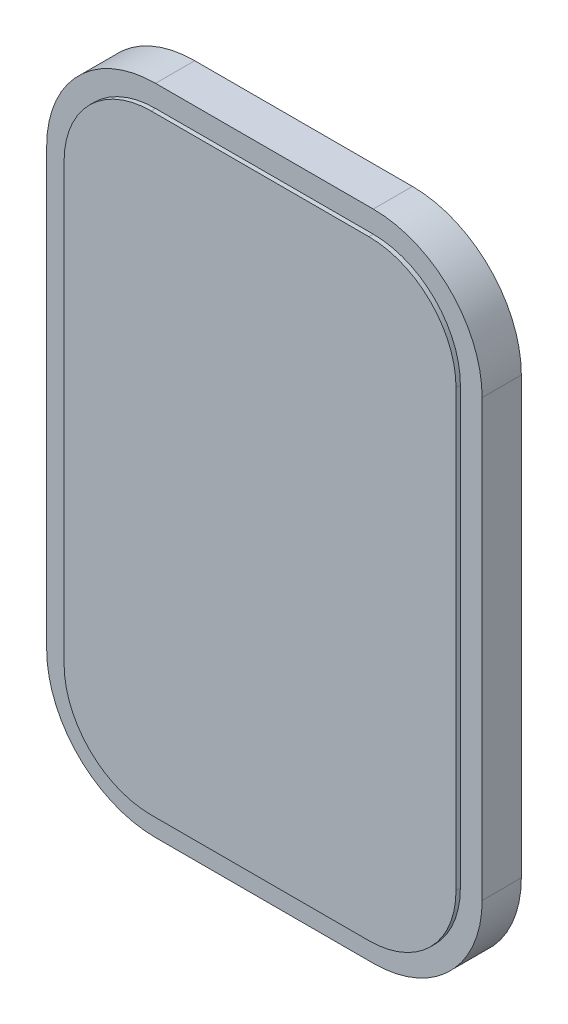
SolidWorks part; units mm, degrees
ref_plane "Front Plane" through (0, 0, 0) normal (0, 0, 1) x (1, 0, 0)
ref_plane "Top Plane" through (0, 0, 0) normal (0, 1, 0) x (1, 0, 0)
ref_plane "Right Plane" through (0, 0, 0) normal (1, 0, 0) x (0, 0, -1)
sketch "Sketch1" plane through (0, 0, 0) normal (0, 0, 1) x (1, 0, 0)
  line L1 (-12.7, -19.05) -> (12.7, -19.05)
  line L2 (-12.7, -19.05) -> (-12.7, 19.05)
  line L3 (-12.7, 19.05) -> (12.7, 19.05)
  line L4 (12.7, -19.05) -> (12.7, 19.05)
  line L5 (-12.7, -19.05) -> (12.7, 19.05) construction
  line L6 (-12.7, 19.05) -> (12.7, -19.05) construction
  point P0 (0, 0)
  dimension "D1" = 25.4
  dimension "D2" = 38.1
extrude "Boss-Extrude1" add sketch "Sketch1" along normal blind 2.54
fillet "Fillet1" radius 6.35 4 edges at (12.7, -19.05, 1.27) (12.7, 19.05, 1.27) (-12.7, -19.05, 1.27) (-12.7, 19.05, 1.27)
sketch "Sketch2" plane through (0, 0, 2.54) normal (0, 0, 1) x (1, 0, 0)
  line L0 (-11.43, 12.7) -> (-11.43, -12.7)
  line L1 (-6.35, -17.78) -> (6.35, -17.78)
  line L2 (11.43, -12.7) -> (11.43, 12.7)
  line L3 (6.35, 17.78) -> (-6.35, 17.78)
  line L4 (-6.35, -19.05) -> (6.35, -19.05)
  line L5 (12.7, -12.7) -> (12.7, 12.7)
  line L6 (6.35, 19.05) -> (-6.35, 19.05)
  line L7 (-12.7, 12.7) -> (-12.7, -12.7)
  line L8 (-6.35, -19.05) -> (6.35, -19.05)
  line L9 (12.7, -12.7) -> (12.7, 12.7)
  line L10 (6.35, 19.05) -> (-6.35, 19.05)
  line L11 (-12.7, 12.7) -> (-12.7, -12.7)
  arc A1 (-6.35, 17.78) -> (-11.43, 12.7) centre (-6.35, 12.7) ccw
  arc A2 (-11.43, -12.7) -> (-6.35, -17.78) centre (-6.35, -12.7) ccw
  arc A3 (6.35, -17.78) -> (11.43, -12.7) centre (6.35, -12.7) ccw
  arc A4 (11.43, 12.7) -> (6.35, 17.78) centre (6.35, 12.7) ccw
  arc A5 (6.35, -19.05) -> (12.7, -12.7) centre (6.35, -12.7) ccw
  arc A6 (12.7, 12.7) -> (6.35, 19.05) centre (6.35, 12.7) ccw
  arc A7 (-6.35, 19.05) -> (-12.7, 12.7) centre (-6.35, 12.7) ccw
  arc A8 (-12.7, -12.7) -> (-6.35, -19.05) centre (-6.35, -12.7) ccw
  arc A9 (6.35, -19.05) -> (12.7, -12.7) centre (6.35, -12.7) ccw
  arc A10 (12.7, 12.7) -> (6.35, 19.05) centre (6.35, 12.7) ccw
  arc A11 (-6.35, 19.05) -> (-12.7, 12.7) centre (-6.35, 12.7) ccw
  arc A12 (-12.7, -12.7) -> (-6.35, -19.05) centre (-6.35, -12.7) ccw
  dimension "D1" = 0
  dimension "D2" = 1.27
extrude "Cut-Extrude1" cut sketch "Sketch2" against normal blind 0.254
sketch "Sketch3" plane through (0, 0, 2.54) normal (0, 0, 1) x (1, 0, 0)
  line L0 (-10.922, 12.7) -> (-10.922, -12.7)
  line L1 (-6.35, -17.272) -> (6.35, -17.272)
  line L2 (10.922, -12.7) -> (10.922, 12.7)
  line L3 (6.35, 17.272) -> (-6.35, 17.272)
  line L4 (-11.43, 12.7) -> (-11.43, -12.7)
  line L5 (-6.35, -17.78) -> (6.35, -17.78)
  line L6 (11.43, -12.7) -> (11.43, 12.7)
  line L7 (6.35, 17.78) -> (-6.35, 17.78)
  line L8 (-11.43, 12.7) -> (-11.43, -12.7)
  line L9 (-6.35, -17.78) -> (6.35, -17.78)
  line L10 (11.43, -12.7) -> (11.43, 12.7)
  line L11 (6.35, 17.78) -> (-6.35, 17.78)
  line L12 (-6.35, 17.272) -> (-6.35, -12.192)
  line L13 (-6.35, -12.192) -> (-10.922, -12.192)
  line L14 (-10.922, -12.7) -> (10.922, -12.7)
  arc A0 (-6.35, 17.272) -> (-10.922, 12.7) centre (-6.35, 12.7) ccw
  arc A1 (-10.922, -12.7) -> (-6.35, -17.272) centre (-6.35, -12.7) ccw
  arc A2 (6.35, -17.272) -> (10.922, -12.7) centre (6.35, -12.7) ccw
  arc A3 (10.922, 12.7) -> (6.35, 17.272) centre (6.35, 12.7) ccw
  arc A4 (-6.35, 17.78) -> (-11.43, 12.7) centre (-6.35, 12.7) ccw
  arc A5 (-11.43, -12.7) -> (-6.35, -17.78) centre (-6.35, -12.7) ccw
  arc A6 (6.35, -17.78) -> (11.43, -12.7) centre (6.35, -12.7) ccw
  arc A7 (11.43, 12.7) -> (6.35, 17.78) centre (6.35, 12.7) ccw
  arc A8 (-6.35, 17.78) -> (-11.43, 12.7) centre (-6.35, 12.7) ccw
  arc A9 (-11.43, -12.7) -> (-6.35, -17.78) centre (-6.35, -12.7) ccw
  arc A10 (6.35, -17.78) -> (11.43, -12.7) centre (6.35, -12.7) ccw
  arc A11 (11.43, 12.7) -> (6.35, 17.78) centre (6.35, 12.7) ccw
  dimension "D3" = 0.508
  dimension "D1" = 0
  dimension "D2" = 0.508
